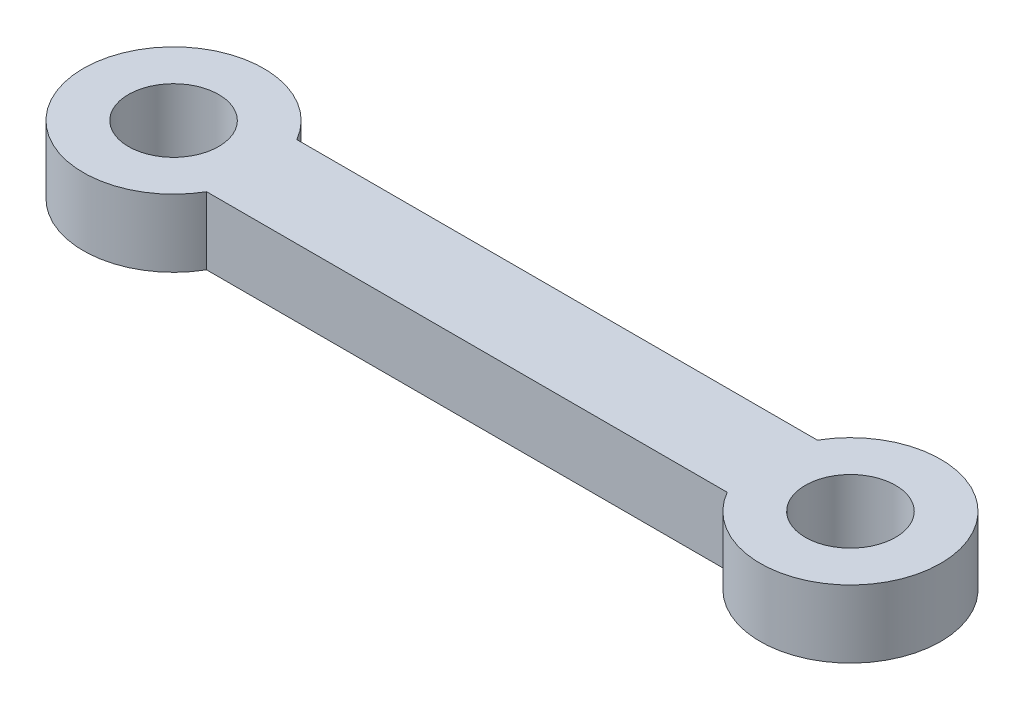
SolidWorks part; units mm, degrees
ref_plane "Front" through (0, 0, 0) normal (0, 0, 1) x (1, 0, 0)
ref_plane "Top" through (0, 0, 0) normal (0, 1, 0) x (1, 0, 0)
ref_plane "Right" through (0, 0, 0) normal (1, 0, 0) x (0, 0, -1)
sketch "Sketch1" plane through (0, 0, 0) normal (0, 1, 0) x (1, 0, 0)
  line L0 (-144.2363, 0) -> (137.1621, 0) construction
  line L1 (0, 85.0876) -> (0, -80.7645) construction
  line L2 (57.6795, 10) -> (-57.6795, 10)
  line L3 (57.6795, -10) -> (-57.6795, -10)
  arc A0 (-57.6795, 10) -> (-57.6795, -10) centre (-75, 0) ccw
  arc A1 (57.6795, 10) -> (57.6795, -10) centre (75, 0) cw
  point P11 (0, -10)
  point P12 (0, 10)
  dimension "D2" = 40
  dimension "D1" = 10
  dimension "D3" = 75
extrude "Boss-Extrude1" add sketch "Sketch1" along normal blind 15
hole_wizard "Ø20.0mm 맞춤핀 구멍1" positions "Sketch3" profile "Sketch2" hole size "Ø20.0" standard "Ansi Metric" end condition through all
sketch "Sketch3" plane through (0, 15, 0) normal (0, 1, 0) x (1, 0, 0)
  arc A0 (-57.6795, 10) -> (-57.6795, -10) centre (-75, 0) ccw construction
  arc A1 (57.6795, -10) -> (57.6795, 10) centre (75, 0) ccw construction
  point P0 (-75, 0)
  point P2 (75, 0)
  dimension "D1" = 0
  dimension "D2" = 0
sketch "Sketch2" plane through (-75, 15, 0) normal (1, 0, 0) x (0, 0, 1)
  line L0 (0, 0) -> (0, 15)
  line L1 (0, 15) -> (10, 15)
  line L2 (10, 15) -> (10, 0)
  line L5 (10, 0) -> (0, 0)
  line L11 (0, -6.35) -> (0, 107.95) construction
  dimension "Thru Hole Dia." = 20
  dimension "Thru Hole Depth" = 15
scale "축척1" scale about centroid uniform scaling yes scale factor 0.3
